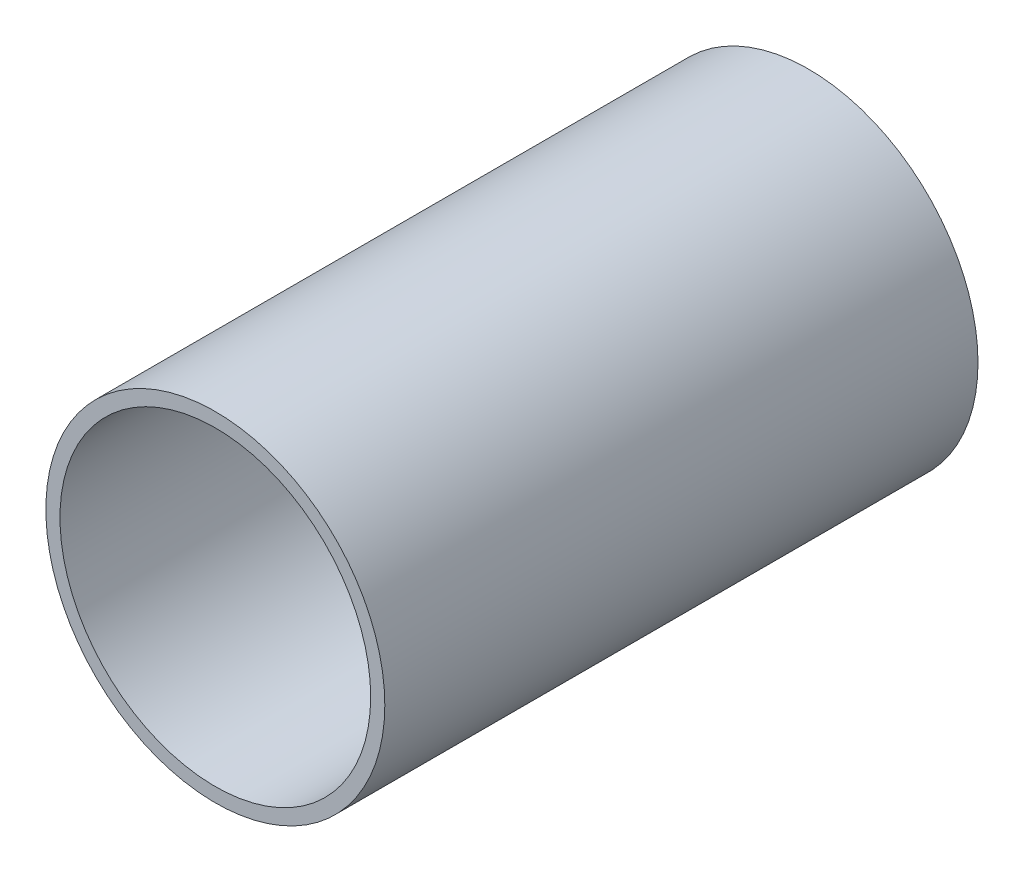
SolidWorks part; units mm, degrees
ref_plane "Front Plane" through (0, 0, 0) normal (0, 0, 1) x (1, 0, 0)
ref_plane "Top Plane" through (0, 0, 0) normal (0, 1, 0) x (1, 0, 0)
ref_plane "Right Plane" through (0, 0, 0) normal (1, 0, 0) x (0, 0, -1)
sketch "Sketch1" plane through (0, 0, 0) normal (0, 0, 1) x (1, 0, 0)
  circle A0 centre (0, 0) radius 11
  circle A1 centre (0, 0) radius 12
  dimension "D1" = 22
  dimension "D2" = 24
extrude "Boss-Extrude1" add sketch "Sketch1" along normal mid plane 42
